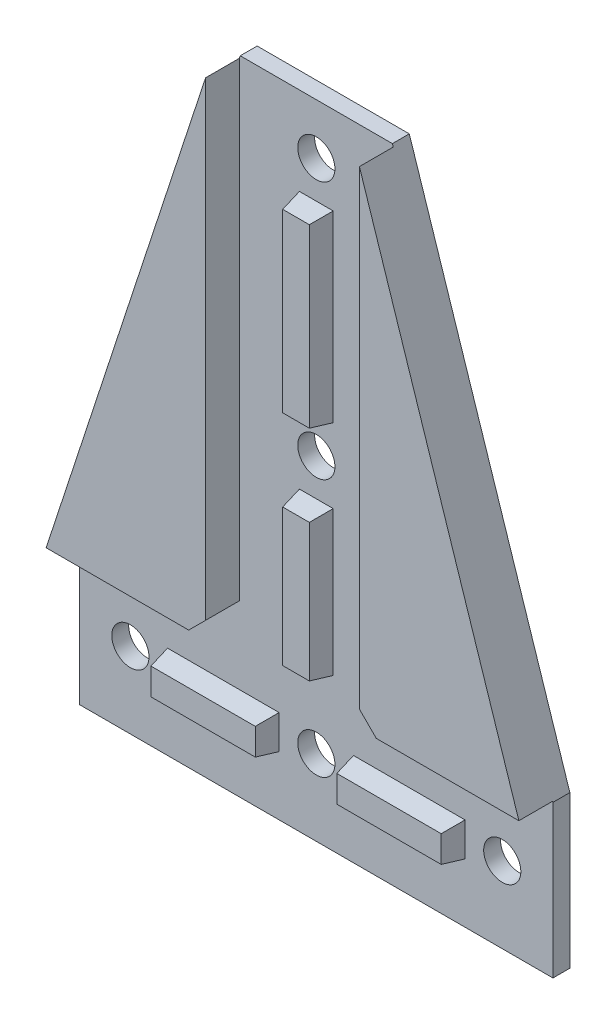
SolidWorks part; units mm, degrees
ref_plane "Plan de face" through (0, 0, 0) normal (0, 0, 1) x (1, 0, 0)
ref_plane "Plan de dessus" through (0, 0, 0) normal (0, 1, 0) x (1, 0, 0)
ref_plane "Plan de droite" through (0, 0, 0) normal (1, 0, 0) x (0, 0, -1)
sketch "Esquisse1" plane through (0, 0, 0) normal (0, 0, 1) x (1, 0, 0)
  line L0 (-22.5, 135.2324) -> (22.5, 135.2324)
  line L1 (22.5, 135.2324) -> (70, -9.7676)
  line L2 (70, -9.7676) -> (70, -54.7676)
  line L3 (70, -54.7676) -> (-70, -54.7676)
  line L4 (0, -54.7676) -> (0, 135.2324) construction
  line L5 (-70, -9.7676) -> (-70, -54.7676)
  line L6 (-22.5, 135.2324) -> (-70, -9.7676)
  line L7 (70, -32.2676) -> (-70, -32.2676) construction
  circle A0 centre (0, 120.2324) radius 5.5
  circle A1 centre (0, 43.9824) radius 5.5
  circle A2 centre (0, -32.2676) radius 5.5
  circle A3 centre (-55, -32.2676) radius 5.5
  circle A4 centre (55, -32.2676) radius 5.5
  dimension "D5" = 11
  dimension "D6" = 11
  dimension "D7" = 11
  dimension "D8" = 22.5
  dimension "D9" = 152.5
  dimension "D10" = 15
  dimension "D11" = 11
  dimension "D12" = 15
  dimension "D13" = 15
  dimension "D14" = 11
  dimension "D15" = 76.25
  dimension "D1" = 22.5
  dimension "D2" = 45
  dimension "D3" = 190
  dimension "D4" = 70
extrude "Boss.-Extru.1" add sketch "Esquisse1" along normal blind 5
sketch "Esquisse3" plane through (0, 0, 5) normal (0, 0, 1) x (1, 0, 0)
  line L0 (0, 120.2324) -> (0, -32.2676) construction
  line L1 (-55, -32.2676) -> (55, -32.2676) construction
  line L2 (-70, -54.7676) -> (70, -54.7676) construction
  line L3 (-5, 109.2324) -> (5, 109.2324)
  line L4 (-5, 109.2324) -> (-5, 54.9824)
  line L5 (-5, 54.9824) -> (5, 54.9824)
  line L6 (5, 109.2324) -> (5, 54.9824)
  line L7 (-5, 32.9824) -> (5, 32.9824)
  line L8 (-5, 32.9824) -> (-5, -9.7676)
  line L9 (-5, -9.7676) -> (5, -9.7676)
  line L10 (5, 32.9824) -> (5, -9.7676)
  line L11 (-44, -27.2676) -> (-11, -27.2676)
  line L12 (-44, -27.2676) -> (-44, -37.2676)
  line L13 (-44, -37.2676) -> (-11, -37.2676)
  line L14 (-11, -27.2676) -> (-11, -37.2676)
  line L15 (11, -27.2676) -> (44, -27.2676)
  line L16 (11, -27.2676) -> (11, -37.2676)
  line L17 (11, -37.2676) -> (44, -37.2676)
  line L18 (44, -27.2676) -> (44, -37.2676)
  point P24 (0, 43.9824)
  dimension "D1" = 10
  dimension "D2" = 10
  dimension "D3" = 10
  dimension "D4" = 10
  dimension "D5" = 5
  dimension "D6" = 11
  dimension "D7" = 11
  dimension "D8" = 5
  dimension "D9" = 11
  dimension "D10" = 45
  dimension "D11" = 5
  dimension "D12" = 11
  dimension "D13" = 11
  dimension "D14" = 11
  dimension "D15" = 11
  dimension "D16" = 5
extrude "Boss.-Extru.3" add sketch "Esquisse3" along normal blind 6
draft "Dépouille2" type of draft neutral plane draft angle 10 faces to draft 16 face at (0, 32.9824, 8) face at (-27.5, -27.2676, 8) face at (27.5, -27.2676, 8) face at (0, 109.2324, 8) face at (-11, -32.2676, 8) face at (44, -32.2676, 8) face at (5, 82.1074, 8) face at (5, 11.6074, 8) face at (-5, 82.1074, 8) face at (0, 54.9824, 8) face at (-5, 11.6074, 8) face at (11, -32.2676, 8) face at (27.5, -37.2676, 8) face at (0, -9.7676, 8) face at (-44, -32.2676, 8) face at (-27.5, -37.2676, 8) neutral plane through (0, 0, 5) neutral plane normal (0, 0, 1) parameters "D1"=10
sketch "Esquisse4" plane through (0, 0, 5) normal (0, 0, 1) x (1, 0, 0)
  line L0 (-22.75, 134.4693) -> (-22.75, -9.5176)
  line L1 (-22.75, -9.5176) -> (-69.9181, -9.5176)
  line L2 (-69.9181, -9.5176) -> (-22.75, 134.4693)
  line L3 (0, 135.2324) -> (0, -32.2676) construction
  line L4 (22.5, 135.2324) -> (-22.5, 135.2324) construction
  line L5 (22.75, -9.5176) -> (69.9181, -9.5176)
  line L6 (22.75, 134.4693) -> (22.75, -9.5176)
  line L7 (69.9181, -9.5176) -> (22.75, 134.4693)
  line L9 (-22.5, 135.2324) -> (-70, -9.7676) construction
  circle A0 centre (-55, -32.2676) radius 5.5 construction
  dimension "D1" = 22.75
  dimension "D2" = 22.75
extrude "Boss.-Extru.4" add sketch "Esquisse4" along normal blind 10
chamfer "Chanfrein1" distance 5 angle 45 2 edges at (22.75, -9.5176, 10) (-22.75, -9.5176, 10)
